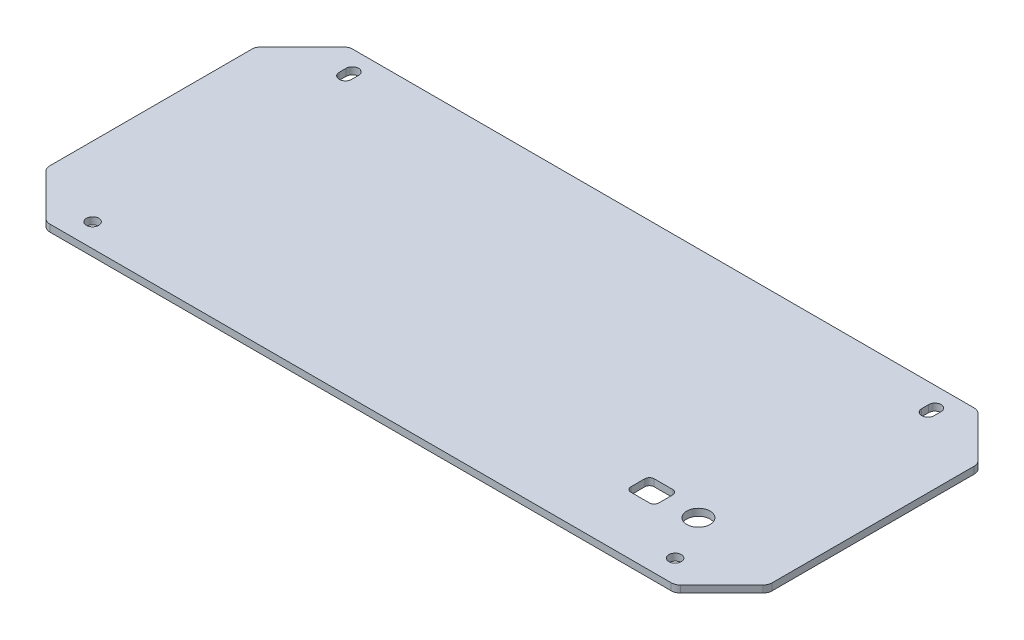
SolidWorks part; units mm, degrees
ref_plane "Front Plane" through (0, 0, 0) normal (0, 0, 1) x (1, 0, 0)
ref_plane "Top Plane" through (0, 0, 0) normal (0, 1, 0) x (1, 0, 0)
ref_plane "Right Plane" through (0, 0, 0) normal (1, 0, 0) x (0, 0, -1)
sketch "Sketch1" plane through (0, 0, 0) normal (0, 1, 0) x (1, 0, 0)
  line L1 (-155, -65) -> (155, -65)
  line L2 (-155, -65) -> (-155, 65)
  line L3 (-155, 65) -> (155, 65)
  line L4 (155, -65) -> (155, 65)
  line L5 (-155, -65) -> (155, 65) construction
  line L6 (-155, 65) -> (155, -65) construction
  point P0 (0, 0)
  dimension "D1" = 310
  dimension "D2" = 130
extrude "Boss-Extrude1" add sketch "Sketch1" along normal blind 3
sketch "Sketch7" plane through (0, 3, 0) normal (0, 1, 0) x (1, 0, 0)
  line L0 (-155, 65) -> (-155, 45)
  line L9 (-155, 65) -> (-155, -65) construction
  line L10 (-155, 45) -> (-135, 65)
  line L11 (155, 65) -> (-155, 65) construction
  line L12 (-135, 65) -> (-155, 65)
  line L13 (0, 0) -> (0, 65) construction
  line L14 (135, 65) -> (155, 65)
  line L15 (155, 45) -> (135, 65)
  line L16 (155, 65) -> (155, 45)
  line L17 (0, 0) -> (155, 0) construction
  line L19 (155, -65) -> (155, -45)
  line L20 (155, -45) -> (135, -65)
  line L21 (135, -65) -> (155, -65)
  line L22 (-135, -65) -> (-155, -65)
  line L23 (-155, -45) -> (-135, -65)
  line L24 (-155, -65) -> (-155, -45)
  dimension "D1" = 20
extrude "Cut-Extrude2" cut sketch "Sketch7" against normal through all
fillet "Fillet1" radius 4 8 edges at (-155, 1.5, -45) (155, 1.5, -45) (135, 1.5, -65) (-135, 1.5, -65) (-135, 1.5, 65) (135, 1.5, 65) (155, 1.5, 45) (-155, 1.5, 45)
hole_wizard "Ø5.3 (5.3) Diameter Hole1" positions "Sketch4" profile "Sketch5" hole size "Ø5.3" standard "ANSI Metric" end condition through all
sketch "Sketch4" plane through (0, 3, 0) normal (0, 1, 0) x (1, 0, 0)
  line L1 (-125, -55) -> (125, -55)
  line L2 (-125, -55) -> (-125, 55)
  line L3 (-125, 55) -> (125, 55)
  line L4 (125, -55) -> (125, 55)
  line L5 (-125, -55) -> (125, 55) construction
  line L6 (-125, 55) -> (125, -55) construction
  line L7 (133.3431, 65) -> (-133.3431, 65) construction
  line L8 (155, -43.3431) -> (155, 43.3431) construction
  point P2 (125, 55)
  point P59 (-125, -55)
  point P60 (-125, 55)
  point P61 (125, -55)
  dimension "D1" = 10
  dimension "D2" = 30
sketch "Sketch5" plane through (125, 3, -55) normal (1, 0, 0) x (0, 0, 1)
  line L0 (0, 0) -> (0, 3)
  line L1 (0, 3) -> (2.65, 3)
  line L2 (2.65, 3) -> (2.65, 0)
  line L5 (2.65, 0) -> (0, 0)
  line L11 (0, -6.35) -> (0, 107.95) construction
  dimension "Thru Hole Dia." = 5.3
  dimension "Thru Hole Depth" = 3
sketch "Sketch6" plane through (0, 3, 0) normal (0, 1, 0) x (1, 0, 0)
  line L0 (-133.3431, -65) -> (133.3431, -65) construction
  line L1 (95, -35) -> (115, -35) construction
  line L2 (89, -40) -> (101, -40)
  line L3 (89, -40) -> (89, -30)
  line L4 (89, -30) -> (101, -30)
  line L5 (101, -40) -> (101, -30)
  line L6 (89, -40) -> (101, -30) construction
  line L7 (89, -30) -> (101, -40) construction
  circle A0 centre (115, -35) radius 5
  point P7 (95, -35)
  dimension "D3" = 10
  dimension "D1" = 115
  dimension "D2" = 30
  dimension "D4" = 10
  dimension "D5" = 12
  dimension "D6" = 95
extrude "Cut-Extrude1" cut sketch "Sketch6" against normal through all
fillet "Fillet2" radius 2 4 edges at (89, 1.5, 40) (89, 1.5, 30) (101, 1.5, 30) (101, 1.5, 40)
sketch "Sketch8" plane through (0, 3, 0) normal (0, 1, 0) x (1, 0, 0)
  line L0 (-125, 53.5) -> (-125, 56.5) construction
  line L1 (-127.65, 53.5) -> (-127.65, 56.5)
  line L2 (-122.35, 53.5) -> (-122.35, 56.5)
  line L3 (125, 53.5) -> (125, 56.5) construction
  line L4 (122.35, 53.5) -> (122.35, 56.5)
  line L5 (127.65, 53.5) -> (127.65, 56.5)
  arc A0 (-127.65, 53.5) -> (-122.35, 53.5) centre (-125, 53.5) ccw
  arc A1 (-122.35, 56.5) -> (-127.65, 56.5) centre (-125, 56.5) ccw
  arc A2 (122.35, 53.5) -> (127.65, 53.5) centre (125, 53.5) ccw
  arc A3 (127.65, 56.5) -> (122.35, 56.5) centre (125, 56.5) ccw
  circle A4 centre (-125, 55) radius 2.65 construction
  point P2 (-125, 55)
  point P9 (125, 55)
  dimension "D1" = 3
extrude "Cut-Extrude3" cut sketch "Sketch8" against normal through all
